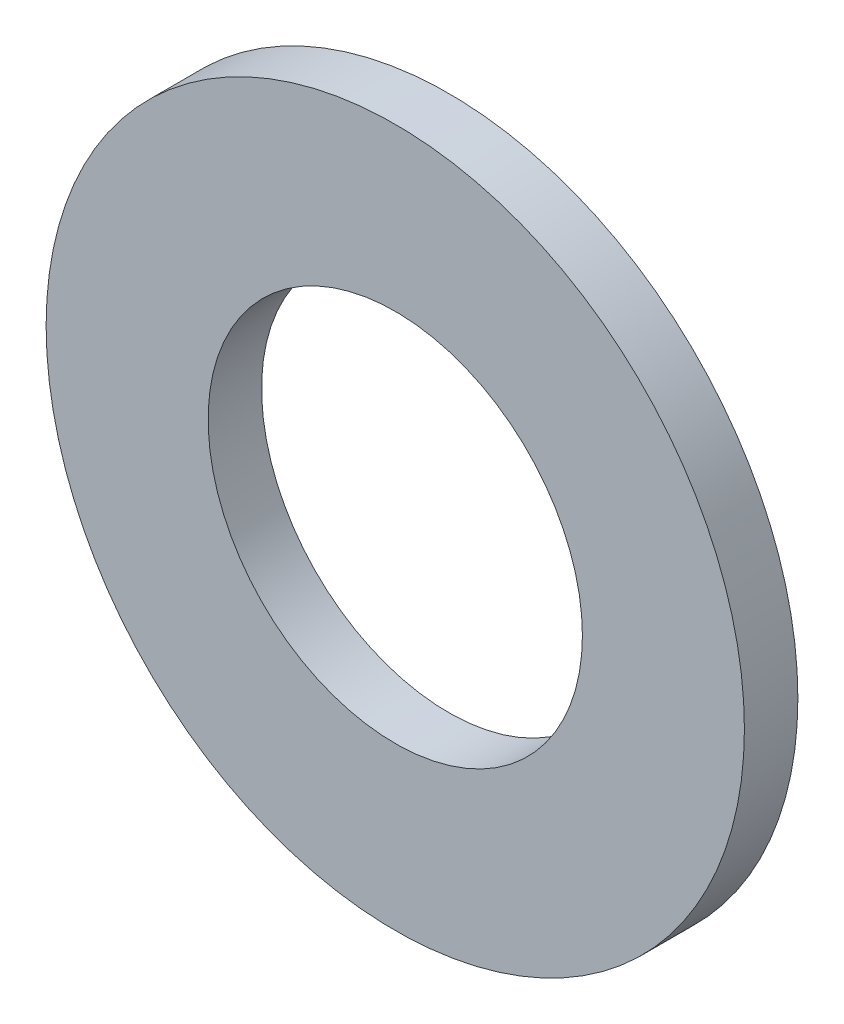
SolidWorks part; units mm, degrees
ref_plane "Top" through (0, 0, 0) normal (0, 0, 1) x (1, 0, 0)
ref_plane "Front" through (0, 0, 0) normal (0, 1, 0) x (1, 0, 0)
ref_plane "Side" through (0, 0, 0) normal (1, 0, 0) x (0, 0, -1)
extrude "Base-Extrude" add sketch "Sketch1" along normal blind 3.4036
sketch "Sketch1" plane through (0, 0, 0) normal (0, 0, 1) x (1, 0, 0)
  circle A0 centre (0, 0) radius 22.225
  circle A1 centre (0, 0) radius 11.9126
  dimension "O.D." = 44.45
  dimension "I.D." = 23.8252
